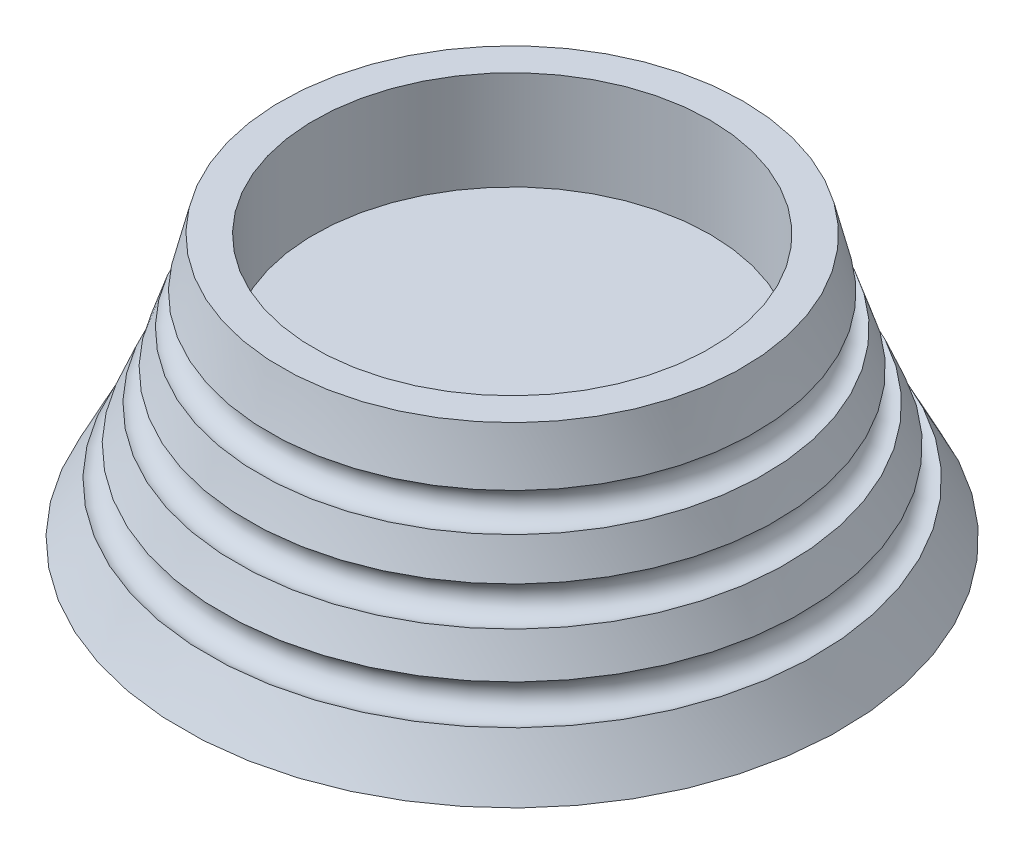
SolidWorks part; units mm, degrees
ref_plane "정면" through (0, 0, 0) normal (0, 0, 1) x (1, 0, 0)
ref_plane "윗면" through (0, 0, 0) normal (0, 1, 0) x (1, 0, 0)
ref_plane "우측면" through (0, 0, 0) normal (1, 0, 0) x (0, 0, -1)
sketch "스케치2" plane through (0, 0, 0) normal (0, 0, 1) x (1, 0, 0)
  line L0 (0, 0) -> (0, 25)
  line L1 (0, 25) -> (30, 25)
  line L2 (30, 25) -> (30, 40)
  line L3 (30, 40) -> (35, 40)
  line L4 (0, 0) -> (50, 0)
  arc A0 (35, 40) -> (36.8744, 32.4051) centre (181.5181, 72.1318) ccw
  arc A1 (36.8744, 32.4051) -> (38.2788, 27.6066) centre (37.5566, 30) ccw
  arc A2 (40.0193, 22.3513) -> (41.757, 17.6632) centre (40.8686, 20) ccw
  arc A3 (43.9745, 12.284) -> (46.0455, 7.7333) centre (44.991, 10) ccw
  arc A4 (38.2788, 27.6066) -> (40.0193, 22.3513) centre (181.5181, 72.1318) ccw
  arc A5 (41.757, 17.6632) -> (43.9745, 12.284) centre (181.5181, 72.1318) ccw
  arc A6 (46.0455, 7.7333) -> (50, 0) centre (181.5181, 72.1318) ccw
  point P14 (0, 0)
  point P15 (0, 0)
  dimension "D4" = 50
  dimension "D5" = 150
  dimension "D7" = 5
  dimension "D8" = 10
  dimension "D1" = 15
  dimension "D2" = 30
  dimension "D3" = 40
  dimension "D6" = 35
  dimension "D9" = 10
  dimension "D10" = 10
revolve "회전1" add sketch "스케치2" angle 360 about L0
